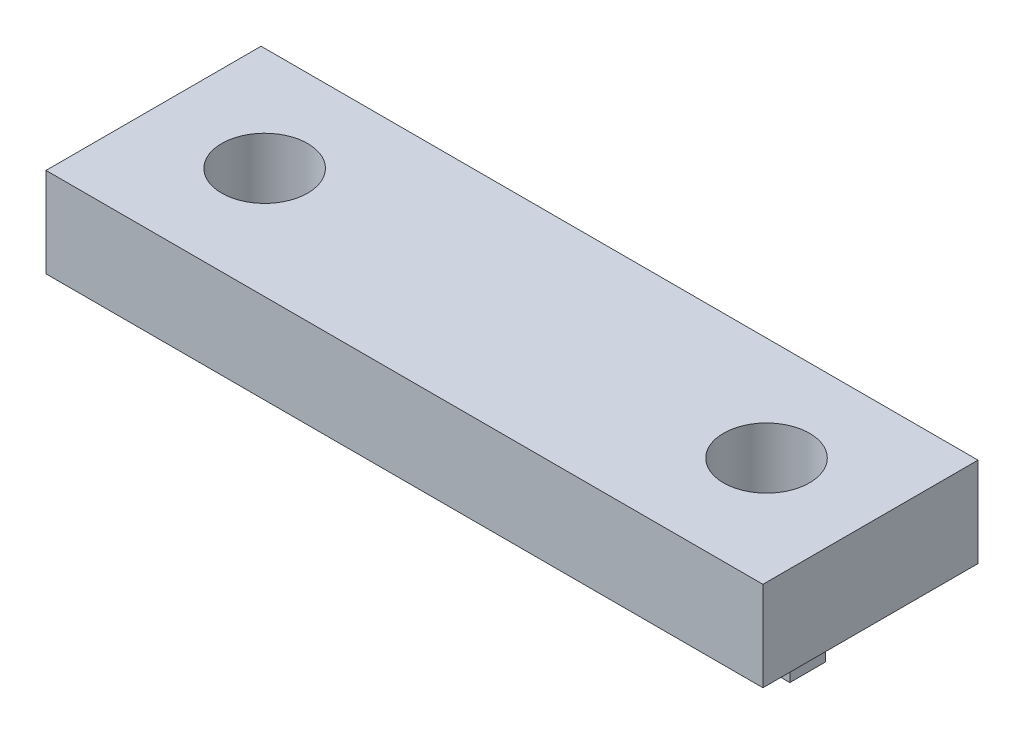
SolidWorks part; units mm, degrees
ref_plane "Plan de face" through (0, 0, 0) normal (0, 0, 1) x (1, 0, 0)
ref_plane "Plan de dessus" through (0, 0, 0) normal (0, 1, 0) x (1, 0, 0)
ref_plane "Plan de droite" through (0, 0, 0) normal (1, 0, 0) x (0, 0, -1)
sketch "Esquisse1" plane through (0, 0, 0) normal (1, 0, 0) x (0, 0, -1)
  line L0 (0, 0) -> (0, 14)
  line L1 (0, 14) -> (-12, 14)
  line L2 (-12, 14) -> (-12, 9)
  line L3 (-12, 9) -> (-2, 9)
  line L4 (-2, 9) -> (-2, 0)
  line L5 (-2, 0) -> (0, 0)
  dimension "D1" = 5
  dimension "D2" = 2
  dimension "D3" = 14
  dimension "D4" = 12
extrude "Boss.-Extru.1" add sketch "Esquisse1" along normal blind 40
sketch "Esquisse2" plane through (0, 14, 0) normal (0, 1, 0) x (1, 0, 0)
  line L0 (0, 0) -> (0, -12) construction
  line L1 (40, 0) -> (40, -12) construction
  line L2 (40, 0) -> (0, 0) construction
  circle A0 centre (34, -5.8) radius 2.4
  circle A1 centre (6, -5.8) radius 2.4
  dimension "D4" = 5.8
  dimension "D5" = 4.8
  dimension "D6" = 4.8
  dimension "D1" = 6
  dimension "D2" = 6
  dimension "D3" = 5.8
extrude "Enlèv. mat.-Extru.1" cut sketch "Esquisse2" against normal blind 40
sketch "Esquisse3" plane through (0, 0, 2) normal (0, 0, 1) x (1, 0, 0)
  line L0 (40, 9) -> (0, 9) construction
  line L1 (0, 0) -> (8.5, 0)
  line L2 (0, 0) -> (0, 9)
  line L3 (0, 9) -> (8.5, 9)
  line L4 (8.5, 0) -> (8.5, 9)
  line L6 (40, 0) -> (31.5, 0)
  line L7 (40, 0) -> (40, 9)
  line L8 (40, 9) -> (31.5, 9)
  line L9 (31.5, 0) -> (31.5, 9)
  dimension "D1" = 23
  dimension "D2" = 8.5
extrude "Enlèv. mat.-Extru.2" cut sketch "Esquisse3" against normal blind 40
sketch "Esquisse4" plane through (0, 0, 2) normal (0, 0, 1) x (1, 0, 0)
  line L0 (31.5, 9) -> (31.5, 0) construction
  line L1 (8.5, 0) -> (8.5, 9) construction
  line L2 (31.5, 0) -> (8.5, 0) construction
  circle A0 centre (26.5, 5) radius 2.5
  circle A1 centre (13.5, 5) radius 2.5
  point P6 (8.5, 4.5)
  dimension "D1" = 5
  dimension "D2" = 5
  dimension "D4" = 5
  dimension "D3" = 5
  dimension "D5" = 5
  dimension "D6" = 5
extrude "Enlèv. mat.-Extru.3" cut sketch "Esquisse4" against normal blind 40
